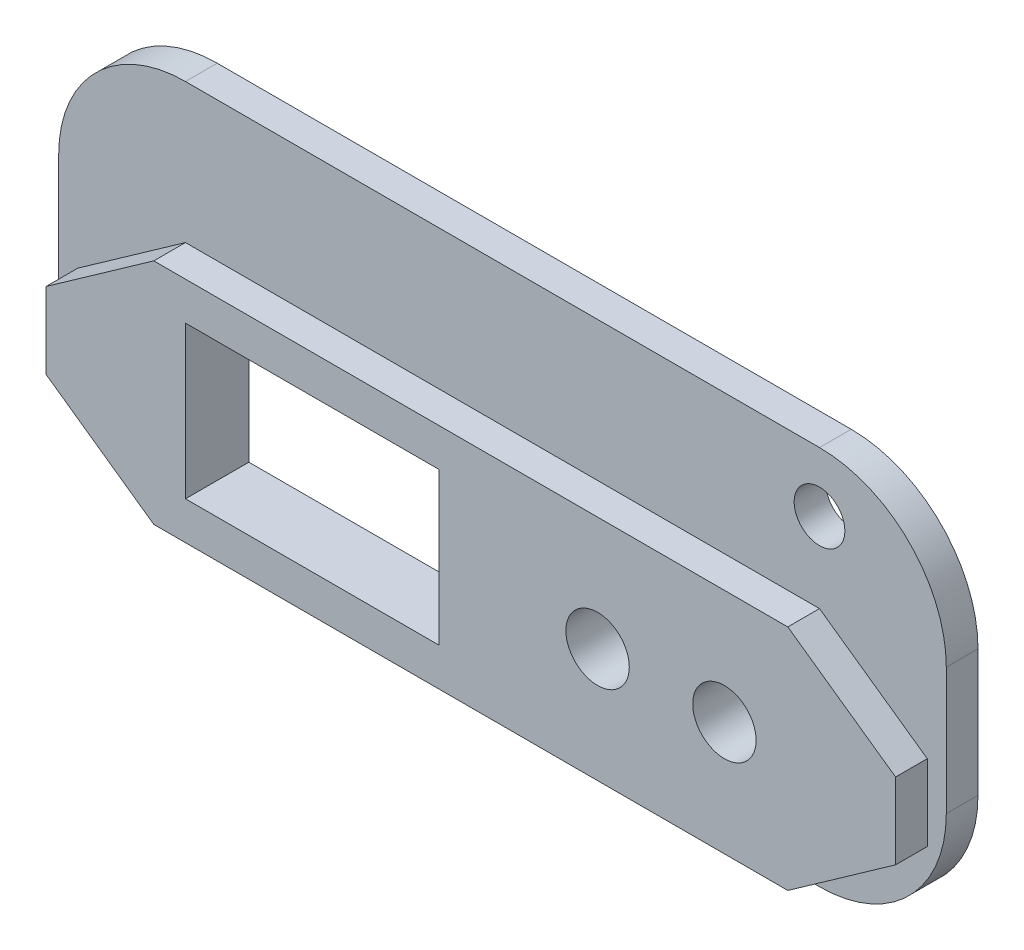
SolidWorks part; units mm, degrees
ref_plane "Front Plane" through (0, 0, 0) normal (0, 0, 1) x (1, 0, 0)
ref_plane "Top Plane" through (0, 0, 0) normal (0, 1, 0) x (1, 0, 0)
ref_plane "Right Plane" through (0, 0, 0) normal (1, 0, 0) x (0, 0, -1)
sketch "Sketch1" plane through (0, 0, 0) normal (0, 0, 1) x (1, 0, 0)
  line L0 (-33.5, 3) -> (-25, 9)
  line L1 (-25, 9) -> (25, 9)
  line L2 (-33.5, 3) -> (-33.5, -3)
  line L3 (-25, -9) -> (25, -9)
  line L4 (33.5, 3) -> (33.5, -3)
  line L5 (-27.3432, 7.3459) -> (27.3432, -7.3459) construction
  line L6 (-27.3432, -7.3459) -> (27.3432, 7.3459) construction
  line L7 (25, 9) -> (33.5, 3)
  line L8 (-33.5, -3) -> (-25, -9)
  line L9 (25, -9) -> (33.5, -3)
  point P0 (0, 0)
  dimension "D1" = 18
  dimension "D2" = 67
  dimension "D3" = 50
  dimension "D4" = 25
  dimension "D5" = 25
  dimension "D6" = 50
  dimension "D7" = 6
  dimension "D8" = 3
  dimension "D9" = 6
  dimension "D10" = 3
extrude "Boss-Extrude1" add sketch "Sketch1" along normal blind 2.5
sketch "Sketch2" plane through (0, 0, 0) normal (0, 0, 1) x (1, 0, 0)
  line L1 (-35, 20) -> (35, 20)
  line L2 (-35, 20) -> (-35, -10)
  line L3 (-35, -10) -> (35, -10)
  line L4 (35, 20) -> (35, -10)
  point P0 (0, 0)
  dimension "D1" = 70
  dimension "D2" = 30
  dimension "D3" = 10
extrude "Boss-Extrude2" add sketch "Sketch2" against normal blind 2.5
sketch "Sketch3" plane through (0, 0, 0) normal (0, 0, 1) x (1, 0, 0)
  line L0 (25, 15.3) -> (25, 9) construction
  circle A0 centre (25, 15.3) radius 2
  dimension "D2" = 4
  dimension "D1" = 6.3
extrude "Cut-Extrude1" cut sketch "Sketch3" against normal blind 2.5
fillet "Fillet1" radius 10 4 edges at (-35, -10, -1.25) (35, -10, -1.25) (35, 20, -1.25) (-35, 20, -1.25)
sketch "Sketch4" plane through (0, 0, 0) normal (0, 0, 1) x (1, 0, 0)
  line L0 (-12.5, 0) -> (0, 0) construction
  line L1 (-22.5, 6) -> (-2.5, 6)
  line L2 (-22.5, 6) -> (-22.5, -6)
  line L3 (-22.5, -6) -> (-2.5, -6)
  line L4 (-2.5, 6) -> (-2.5, -6)
  line L5 (-22.5, 6) -> (-2.5, -6) construction
  line L6 (-22.5, -6) -> (-2.5, 6) construction
  line L7 (0, 0) -> (10, 0) construction
  line L8 (10, 0) -> (20, 0) construction
  circle A0 centre (10, 0) radius 2.5
  circle A1 centre (20, 0) radius 2.5
  point P0 (-12.5, 0)
  dimension "D4" = 5
  dimension "D5" = 5
  dimension "D7" = 10
  dimension "D1" = 12.5
  dimension "D2" = 20
  dimension "D3" = 12
  dimension "D6" = 10
extrude "Cut-Extrude2" cut sketch "Sketch4" against normal through all both and the other way through all
